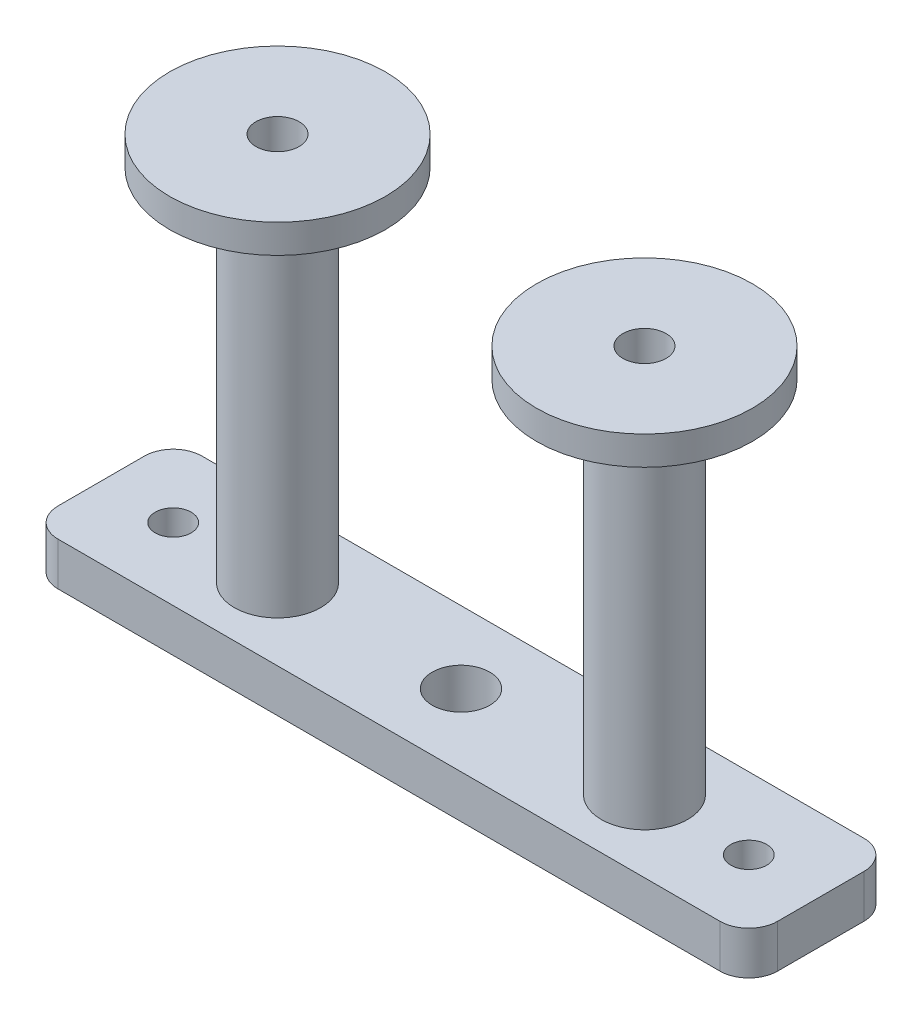
SolidWorks part; units mm, degrees
ref_plane "Front Plane" through (0, 0, 0) normal (0, 0, 1) x (1, 0, 0)
ref_plane "Top Plane" through (0, 0, 0) normal (0, 1, 0) x (1, 0, 0)
ref_plane "Right Plane" through (0, 0, 0) normal (1, 0, 0) x (0, 0, -1)
sketch "Sketch1" plane through (0, 0, 0) normal (0, 1, 0) x (1, 0, 0)
  line L1 (2, 0) -> (48, 0)
  line L2 (0, 2) -> (0, 8)
  line L3 (2, 10) -> (48, 10)
  line L4 (50, 2) -> (50, 8)
  arc A0 (0, 2) -> (2, 0) centre (2, 2) ccw
  arc A1 (48, 0) -> (50, 2) centre (48, 2) ccw
  arc A2 (48, 10) -> (50, 8) centre (48, 8) cw
  arc A3 (2, 10) -> (0, 8) centre (2, 8) ccw
  point P7 (0, 0)
  point P10 (50, 0)
  point P13 (50, 10)
  dimension "D3" = 2
  dimension "D1" = 10
  dimension "D2" = 50
extrude "Boss-Extrude8" add sketch "Sketch1" along normal blind 3
sketch "Sketch15" plane through (0, 3, 0) normal (0, 1, 0) x (1, 0, 0)
  line L0 (0, 5) -> (50, 5)
  line L1 (0, 8) -> (0, 2) construction
  line L2 (50, 2) -> (50, 8) construction
  line L3 (0, 5) -> (5, 5)
  line L4 (50, 5) -> (45, 5)
  circle A0 centre (5, 5) radius 1.25
  circle A1 centre (45, 5) radius 1.25
  dimension "D1" = 5
  dimension "D2" = 5
extrude "Cut-Extrude8" cut sketch "Sketch15" against normal blind 3 contours L0 A0 L3 | L3 A0 L0 | L0 A1 | L0 A1
sketch "Sketch16" plane through (0, 3, 0) normal (0, 1, 0) x (1, 0, 0)
  line L0 (0, 5) -> (50, 5)
  line L1 (0, 8) -> (0, 2) construction
  line L2 (50, 2) -> (50, 8) construction
  line L3 (6.25, 5) -> (12.25, 5)
  line L4 (43.75, 5) -> (37.75, 5)
  circle A0 centre (5, 5) radius 1.25 construction
  circle A1 centre (45, 5) radius 1.25 construction
  circle A2 centre (12.25, 5) radius 3
  circle A3 centre (37.75, 5) radius 3
  dimension "D1" = 6
  dimension "D2" = 6
extrude "Boss-Extrude9" add sketch "Sketch16" along normal blind 25 contours L0 A2 L3 | L3 A2 L0 | L0 A3 | L0 A3
sketch "Sketch17" plane through (0, 28, 0) normal (0, 1, 0) x (1, 0, 0)
  circle A0 centre (12.25, 5) radius 7.5
extrude "Boss-Extrude10" add sketch "Sketch17" along normal blind 2
sketch "Sketch18" plane through (0, 30, 0) normal (0, 1, 0) x (1, 0, 0)
  circle A0 centre (12.25, 5) radius 1.5
extrude "Cut-Extrude9" cut sketch "Sketch18" against normal blind 62
sketch "Sketch19" plane through (0, 28, 0) normal (0, 1, 0) x (1, 0, 0)
  circle A0 centre (37.75, 5) radius 7.5
extrude "Boss-Extrude11" add sketch "Sketch19" along normal blind 2
sketch "Sketch21" plane through (0, 30, 0) normal (0, 1, 0) x (1, 0, 0)
  circle A0 centre (37.75, 5) radius 1.5
extrude "Cut-Extrude10" cut sketch "Sketch21" against normal blind 52
sketch "Sketch23" plane through (0, 0, 0) normal (0, -1, 0) x (1, 0, 0)
  line L0 (0, -5) -> (50, -5)
  line L1 (0, -8) -> (0, -2) construction
  line L2 (50, -2) -> (50, -8) construction
  circle A0 centre (25, -5) radius 2
extrude "Cut-Extrude11" cut sketch "Sketch23" against normal blind 22 contours L0 A0 | L0 A0
